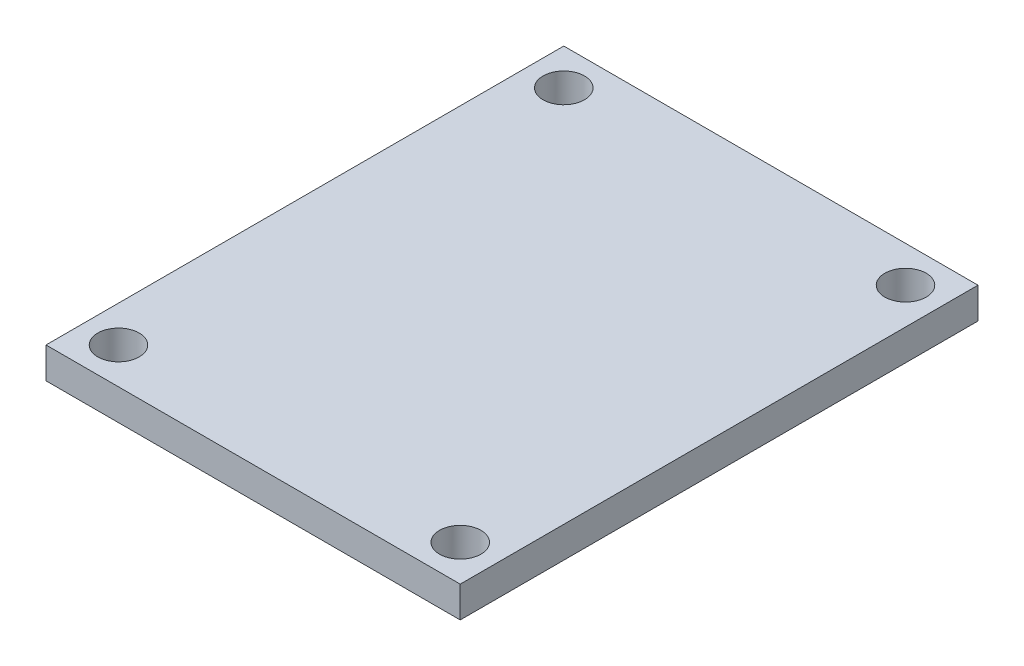
SolidWorks part; units mm, degrees
ref_plane "Alzado" through (0, 0, 0) normal (0, 0, 1) x (1, 0, 0)
ref_plane "Planta" through (0, 0, 0) normal (0, 1, 0) x (1, 0, 0)
ref_plane "Vista lateral" through (0, 0, 0) normal (1, 0, 0) x (0, 0, -1)
sketch "Croquis2" plane through (0, 0, 0) normal (0, 1, 0) x (1, 0, 0)
  line L1 (-254, -317.5) -> (254, -317.5)
  line L2 (-254, -317.5) -> (-254, 317.5)
  line L3 (-254, 317.5) -> (254, 317.5)
  line L4 (254, -317.5) -> (254, 317.5)
  line L5 (-254, -317.5) -> (254, 317.5) construction
  line L6 (-254, 317.5) -> (254, -317.5) construction
  point P0 (0, 0)
  dimension "D1" = 635
  dimension "D2" = 508
extrude "Saliente-Extruir2" add sketch "Croquis2" along normal blind 38.1
sketch "Croquis3" plane through (0, 38.1, 0) normal (0, 1, 0) x (1, 0, 0)
  line L0 (254, 317.5) -> (-254, 317.5) construction
  line L1 (-254, 317.5) -> (-254, -317.5) construction
  line L3 (0, 317.5) -> (0, -317.5) construction
  line L4 (-254, -317.5) -> (254, -317.5) construction
  line L5 (-254, 0) -> (254, 0) construction
  line L6 (254, -317.5) -> (254, 317.5) construction
  circle A0 centre (-209.55, 273.05) radius 25.4
  circle A1 centre (209.55, 273.05) radius 25.4
  circle A2 centre (209.55, -273.05) radius 25.4
  circle A3 centre (-209.55, -273.05) radius 25.4
  dimension "D1" = 50.8
  dimension "D3" = 44.45
  dimension "D2" = 44.45
extrude "Cortar-Extruir1" cut sketch "Croquis3" against normal up to surface (38.1 mm away) up to face at (0, 0, 0)
